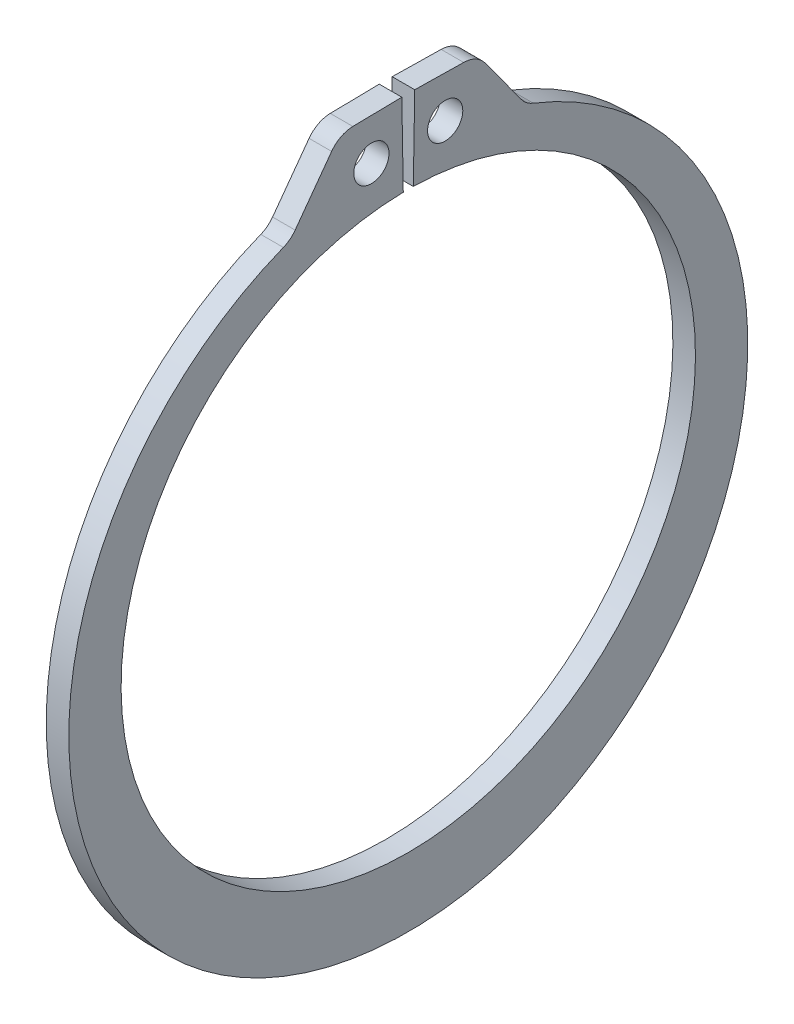
SolidWorks part; units mm, degrees
material "Cast Carbon Steel"
ref_plane "Front" through (0, 0, 0) normal (0, 0, 1) x (1, 0, 0)
ref_plane "Top" through (0, 0, 0) normal (0, 1, 0) x (1, 0, 0)
ref_plane "Right" through (0, 0, 0) normal (1, 0, 0) x (0, 0, -1)
sketch "Sketch1" plane through (0, 0, 0) normal (1, 0, 0) x (0, 0, -1)
  line L0 (0, 0) -> (0, 16.1544) construction
  line L1 (-0.2819, 16.1519) -> (-0.3635, 20.8248)
  line L2 (0.3635, 20.8248) -> (3.8682, 20.7637)
  line L3 (3.8682, 20.7637) -> (6.6264, 16.9908)
  line L4 (0.2819, 16.1519) -> (0.3635, 20.8248)
  line L5 (-0.3635, 20.8248) -> (-3.8682, 20.7637)
  line L6 (-3.8682, 20.7637) -> (-6.6264, 16.9908)
  line L7 (-6.6264, 16.9908) -> (-5.8696, 15.0503) construction
  line L8 (6.6264, 16.9908) -> (5.8696, 15.0503) construction
  line L9 (0, -16.1544) -> (0, -20.0152) construction
  line L10 (-3.8682, 20.7637) -> (-0.2819, 16.1519) construction
  line L11 (0, 16.1544) -> (0, 20.828) construction
  line L12 (-16.1544, 0) -> (16.1544, 0) construction
  circle A0 centre (0, 0) radius 16.1544 construction
  arc A1 (-0.2819, 16.1519) -> (0.2819, 16.1519) centre (0, 0) ccw
  circle A3 centre (0, 0) radius 22.352 construction
  circle A4 centre (-2.075, 18.4578) radius 0.9906
  circle A5 centre (2.075, 18.4578) radius 0.9906
  arc A6 (-6.6264, 16.9908) -> (6.6264, 16.9908) centre (0, -0.9189) ccw
  point P0 (0, -20.0152)
  dimension "A" = 32.3088
  dimension "Hole" = 1.9812
  dimension "Smin" = 2.0828
  dimension "H" = 4.6736
  dimension "D2" = 3.5052
  dimension "Angle" = 1
extrude "Extrude1" add sketch "Sketch1" along normal mid plane 1.27
fillet "Fillet1" radius 1.5113 4 edges at (0, 16.9908, 6.6264) (0, 16.9908, -6.6264) (0, 20.7637, 3.8682) (0, 20.7637, -3.8682)
sketch "Sketch2" plane through (0, 0, 0) normal (0, 0, 1) x (1, 0, 0)
  line L0 (-7.0612, 0) -> (18.3388, 0)
  line L1 (18.3388, 0) -> (18.3388, -17.4625)
  line L2 (-0.7112, -17.4625) -> (-5.9944, -17.4625)
  line L3 (18.3388, -17.4625) -> (0.7112, -17.4625)
  line L4 (0.7112, -17.4625) -> (0.7112, -16.3957)
  line L5 (0.7112, -16.3957) -> (-0.7112, -16.3957)
  line L6 (-0.7112, -16.3957) -> (-0.7112, -17.4625)
  line L7 (-0.7112, -17.4625) -> (-7.0612, -17.4625) construction
  line L8 (-7.0612, -17.4625) -> (-7.0612, 0) construction
  line L9 (18.3388, 0) -> (76.391, 0) construction
  line L10 (-5.9944, -17.4625) -> (-7.0612, -16.3957)
  line L11 (-7.0612, -16.3957) -> (-7.0612, 0)
  point P10 (0, -16.3957)
  dimension "D2" = 25.4
  dimension "D3" = 6.35
  dimension "D1" = 45
revolve "Revolve1" [suppressed] add sketch "Sketch2" angle 360 about L9
delete or keep bodies "Body-Delete1" [suppressed] type delete bodies bodies 122
equation "\"D2@Sketch2\" = \"D1@Extrude1\"*20"
equation "\"D3@Sketch2\" = \"D2@Sketch2\"/4"
equation "\"D2@Sketch1\" = \"H@Sketch1\"*.75"
